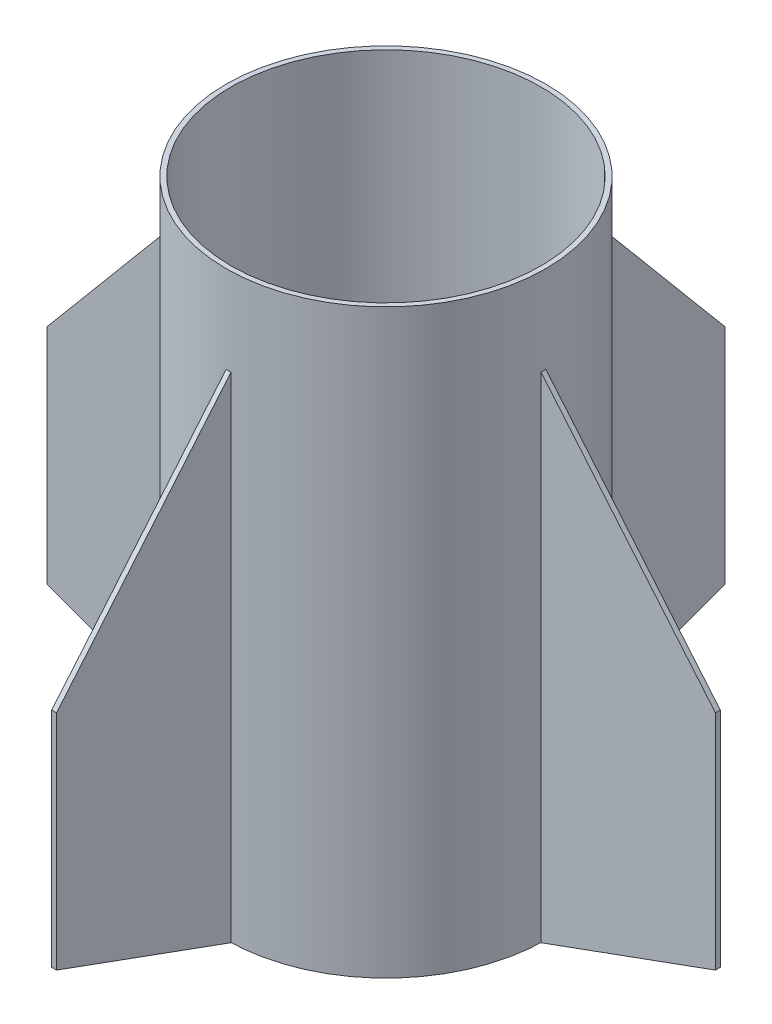
SolidWorks part; units mm, degrees
ref_plane "Front Plane" through (0, 0, 0) normal (0, 0, 1) x (1, 0, 0)
ref_plane "Top Plane" through (0, 0, 0) normal (0, 1, 0) x (1, 0, 0)
ref_plane "Right Plane" through (0, 0, 0) normal (1, 0, 0) x (0, 0, -1)
sketch "Sketch1" plane through (0, 0, 0) normal (0, 1, 0) x (1, 0, 0)
  circle A0 centre (0, 0) radius 101.6
  circle A1 centre (0, 0) radius 104.775
  dimension "D1" = 203.2
  dimension "D2" = 209.55
extrude "Boss-Extrude1" add sketch "Sketch1" along normal blind 381
sketch "Sketch2" plane through (0, 0, 0) normal (1, 0, 0) x (0, 0, -1)
  line L0 (-104.775, 323.85) -> (-219.075, 187.6577)
  line L1 (-104.775, 381) -> (-104.775, 0) construction
  line L2 (-219.075, 187.6577) -> (-219.075, 41.6077)
  line L3 (-219.075, 41.6077) -> (-104.775, 0)
  line L4 (-104.775, 0) -> (-104.775, 323.85)
  line L5 (0, 0) -> (0, 544.109) construction
  dimension "D1" = 114.3
  dimension "D2" = 177.8
  dimension "D3" = 323.85
  dimension "D4" = 146.05
extrude "Boss-Extrude2" add sketch "Sketch2" along normal blind 3.175 separate body
sketch "Sketch5" plane through (0, 0, 0) normal (1, 0, 0) x (0, 0, -1)
  line L0 (104.775, 323.85) -> (219.075, 187.6577)
  line L1 (104.775, 0) -> (104.775, 381) construction
  line L2 (219.075, 187.6577) -> (219.075, 41.6077)
  line L3 (219.075, 41.6077) -> (104.775, 0)
  line L4 (104.775, 0) -> (104.775, 381) construction
  line L5 (104.775, 323.85) -> (104.775, 0)
  dimension "D1" = 323.85
  dimension "D2" = 177.8
  dimension "D3" = 114.3
  dimension "D4" = 146.05
extrude "Boss-Extrude3" add sketch "Sketch5" along normal blind 3.175 separate body
sketch "Sketch6" plane through (0, 0, 0) normal (0, 0, 1) x (1, 0, 0)
  line L0 (-104.775, 323.85) -> (-219.075, 187.6577)
  line L1 (-104.775, 381) -> (-104.775, 0) construction
  line L2 (-219.075, 187.6577) -> (-219.075, 41.6077)
  line L3 (-219.075, 41.6077) -> (-104.775, 0)
  line L4 (-104.775, 323.85) -> (-104.775, 0)
  dimension "D1" = 146.05
  dimension "D2" = 177.8
  dimension "D3" = 323.85
  dimension "D4" = 114.3
extrude "Boss-Extrude4" add sketch "Sketch6" along normal blind 3.175 separate body
sketch "Sketch7" plane through (0, 0, 0) normal (0, 0, 1) x (1, 0, 0)
  line L0 (104.775, 323.85) -> (219.075, 187.6577)
  line L1 (104.775, 0) -> (104.775, 381) construction
  line L2 (219.075, 187.6577) -> (219.075, 41.6077)
  line L3 (219.075, 41.6077) -> (104.775, 0)
  line L4 (104.775, 0) -> (104.775, 323.85)
  dimension "D1" = 114.3
  dimension "D2" = 146.05
  dimension "D3" = 177.8
  dimension "D4" = 323.85
extrude "Boss-Extrude5" add sketch "Sketch7" along normal blind 3.175 separate body
